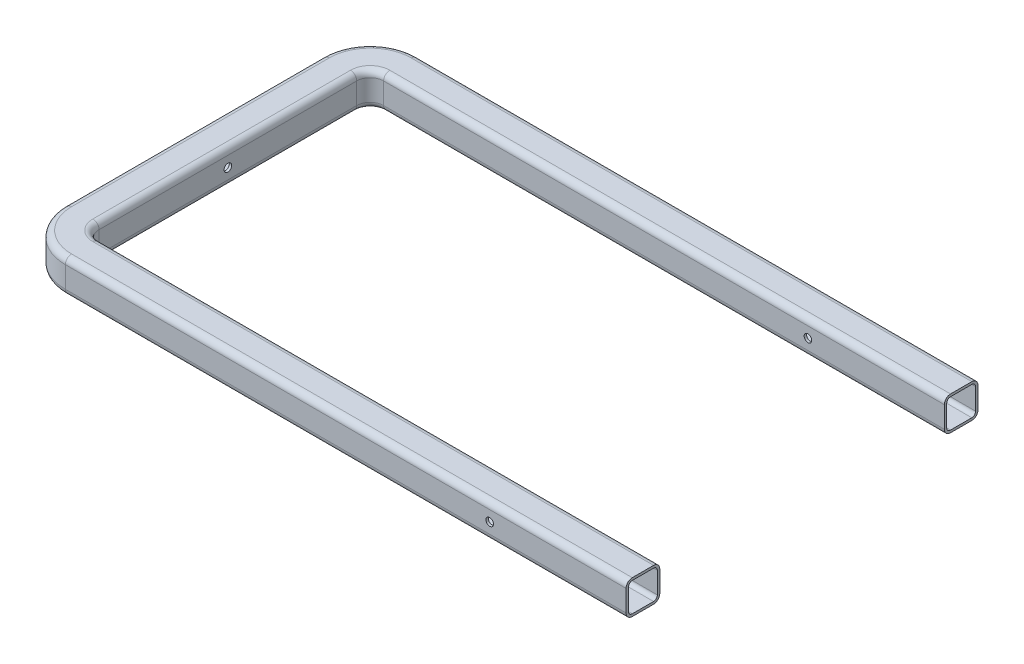
SolidWorks part; units mm, degrees
material "5052-H38, Rod (SS)"
ref_plane "Front Plane" through (0, 0, 0) normal (0, 0, 1) x (1, 0, 0)
ref_plane "Top Plane" through (0, 0, 0) normal (0, 1, 0) x (1, 0, 0)
ref_plane "Right Plane" through (0, 0, 0) normal (1, 0, 0) x (0, 0, -1)
sketch "Sketch1" plane through (0, 0, 0) normal (0, 1, 0) x (1, 0, 0)
  line L0 (0, 0) -> (-610, 0)
  line L1 (-650, 40) -> (-650, 380)
  line L2 (-610, 420) -> (0, 420)
  line L3 (-50, 0) -> (-50, 420) construction
  line L4 (-650, 210) -> (-657.5631, 210) construction
  line L5 (0, 0) -> (130, 0)
  line L6 (0, 420) -> (130, 420)
  arc A0 (-610, 0) -> (-650, 40) centre (-610, 40) cw
  arc A1 (-610, 420) -> (-650, 380) centre (-610, 380) ccw
  point P7 (-650, 0)
  point P10 (-650, 420)
  dimension "D3" = 40
  dimension "D1" = 650
  dimension "D2" = 420
  dimension "D4" = 50
  dimension "D5" = 130
  dimension "D6" = 130
sketch "Sketch2" plane through (0, 0, 0) normal (1, 0, 0) x (0, 0, -1)
  line L1 (-14.05, -19.05) -> (14.05, -19.05)
  line L2 (-19.05, -14.05) -> (-19.05, 14.05)
  line L3 (-14.05, 19.05) -> (14.05, 19.05)
  line L4 (19.05, -14.05) -> (19.05, 14.05)
  line L5 (-19.05, -19.05) -> (19.05, 19.05) construction
  line L6 (-19.05, 19.05) -> (19.05, -19.05) construction
  arc A0 (-14.05, 19.05) -> (-19.05, 14.05) centre (-14.05, 14.05) ccw
  arc A1 (-19.05, -14.05) -> (-14.05, -19.05) centre (-14.05, -14.05) ccw
  arc A2 (14.05, -19.05) -> (19.05, -14.05) centre (14.05, -14.05) ccw
  arc A3 (19.05, 14.05) -> (14.05, 19.05) centre (14.05, 14.05) ccw
  point P0 (0, 0)
  dimension "D3" = 5
  dimension "D1" = 38.1
  dimension "D2" = 38.1
sweep "Sweep-Thin1" add profiles "Sketch2" path "Sketch1" parameters "D1"=3.175
sketch "Sketch3" plane through (0, 0, 0) normal (0, 0, 1) x (1, 0, 0)
  line L0 (0, 0) -> (-610, 0) construction
  circle A0 centre (-50, 0) radius 5
  dimension "D1" = 50
extrude "Cut-Extrude1" cut sketch "Sketch3" against normal through all and the other way through all
sketch "Sketch4" plane through (0, 0, -22.225) normal (0, 0, -1) x (-1, 0, 0)
  line L0 (0, 0) -> (45, 0) construction
  circle A0 centre (50, 0) radius 5 construction
ref_plane "Plane1" through (-650, 0, 0) normal (1, 0, 0) x (0, 0, -1)
sketch "Sketch5" plane through (-650, 0, 0) normal (1, 0, 0) x (0, 0, -1)
  line L0 (380, 0) -> (38.7593, 0) construction
  line L1 (209.3797, 0) -> (281.8797, 0) construction
  line L3 (209.3797, 0) -> (136.8797, 0) construction
  line L4 (281.8797, 0) -> (281.8797, -50) construction
  line L5 (136.8797, 0) -> (136.8797, -50) construction
  dimension "D1" = 72.5
  dimension "D2" = 72.5
ref_plane "Plane2" through (0, 0, -210) normal (0, 0, -1) x (-1, 0, 0)
sketch "Sketch6" plane through (-672.225, 0, 0) normal (-1, 0, 0) x (0, 0, 1)
  line L0 (-40, 0) -> (-380, 0) construction
  line L1 (-40, 14.05) -> (-40, -14.05) construction
  line L2 (-380, 14.05) -> (-380, -14.05) construction
  circle A0 centre (-210, 0) radius 5
extrude "Cut-Extrude2" cut sketch "Sketch6" against normal through all
